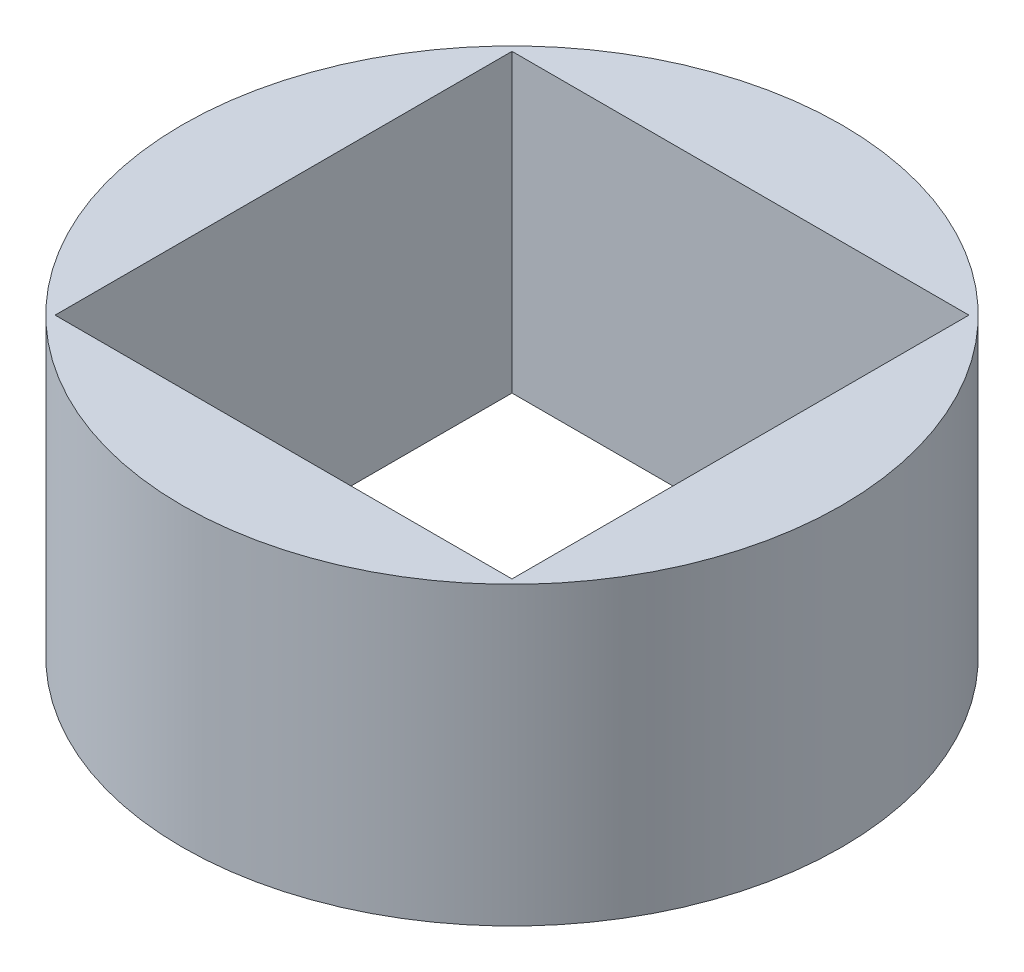
SolidWorks part; units mm, degrees
ref_plane "Front Plane" through (0, 0, 0) normal (0, 0, 1) x (1, 0, 0)
ref_plane "Top Plane" through (0, 0, 0) normal (0, 1, 0) x (1, 0, 0)
ref_plane "Right Plane" through (0, 0, 0) normal (1, 0, 0) x (0, 0, -1)
sketch "Sketch1" plane through (0, 0, 0) normal (0, 1, 0) x (1, 0, 0)
  line L9 (-0.9, -0.9) -> (0.9, 0.9) construction
  line L10 (-0.9, 0.9) -> (0.9, -0.9) construction
  circle A0 centre (0, 0) radius 1.27
extrude "Boss-Extrude1" add sketch "Sketch1" along normal blind 1.14
sketch "Sketch2" plane through (0, 1.14, 0) normal (0, 1, 0) x (1, 0, 0)
  line L1 (-0.88, -0.88) -> (0.88, -0.88)
  line L2 (-0.88, -0.88) -> (-0.88, 0.88)
  line L3 (-0.88, 0.88) -> (0.88, 0.88)
  line L4 (0.88, -0.88) -> (0.88, 0.88)
  line L5 (-0.88, -0.88) -> (0.88, 0.88) construction
  line L6 (-0.88, 0.88) -> (0.88, -0.88) construction
  point P0 (0, 0)
  dimension "D1" = 1.76
  dimension "D2" = 1.76
extrude "Cut-Extrude2" cut sketch "Sketch2" against normal blind 1.14
